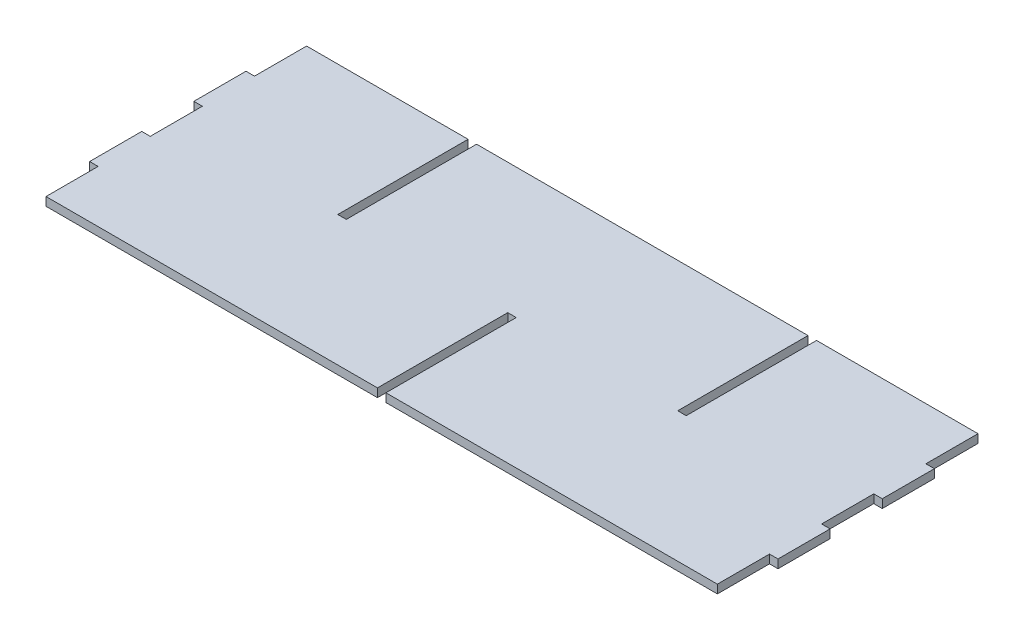
SolidWorks part; units mm, degrees
ref_plane "Piano frontale" through (0, 0, 0) normal (0, 0, 1) x (1, 0, 0)
ref_plane "Piano superiore" through (0, 0, 0) normal (0, 1, 0) x (1, 0, 0)
ref_plane "Piano destro" through (0, 0, 0) normal (1, 0, 0) x (0, 0, -1)
sketch "Schizzo4" plane through (0, 0, 0) normal (0, 1, 0) x (1, 0, 0)
  line L0 (61.5, 46) -> (61.5, -46) construction
  line L2 (-118.5, -46) -> (-118.5, 46) construction
  line L3 (-61.5, 46) -> (-118.5, 46)
  line L4 (118.5, -46) -> (118.5, 46) construction
  line L5 (-118.5, -46) -> (118.5, 46) construction
  line L6 (-118.5, 46) -> (118.5, -46) construction
  line L7 (58.5, 46) -> (58.5, -46) construction
  line L8 (1.5, 46) -> (1.5, -46) construction
  line L9 (-1.5, 46) -> (-1.5, -46) construction
  line L10 (-58.5, 46) -> (-58.5, -46) construction
  line L11 (-61.5, 46) -> (-61.5, -46) construction
  line L12 (-118.5, 46) -> (-118.5, -46) construction
  line L14 (58.5, 46) -> (1.5, 46) construction
  line L15 (-118.5, 0) -> (118.5, 0) construction
  line L19 (-61.5, 46) -> (-61.5, 0)
  line L20 (-61.5, 0) -> (-58.5, 0)
  line L21 (-58.5, 0) -> (-58.5, 46)
  line L22 (-118.5, -46) -> (-1.5, -46)
  line L23 (-58.5, 46) -> (58.5, 46)
  line L24 (1.5, -46) -> (118.5, -46)
  line L25 (61.5, 46) -> (118.5, 46)
  line L26 (-1.5, -46) -> (-1.5, 0)
  line L27 (-1.5, 0) -> (1.5, 0)
  line L28 (1.5, 0) -> (1.5, -46)
  line L29 (58.5, 46) -> (58.5, 0)
  line L30 (58.5, 0) -> (61.5, 0)
  line L31 (61.5, 0) -> (61.5, 46)
  line L32 (-118.5, -46) -> (-118.5, -27.6)
  line L33 (-118.5, -27.6) -> (-121.5, -27.6)
  line L34 (-121.5, -27.6) -> (-121.5, -9.2)
  line L35 (-121.5, -9.2) -> (-118.5, -9.2)
  line L36 (-118.5, -9.2) -> (-118.5, 9.2)
  line L37 (-118.5, 9.2) -> (-121.5, 9.2)
  line L38 (-121.5, 9.2) -> (-121.5, 27.6)
  line L39 (-121.5, 27.6) -> (-118.5, 27.6)
  line L40 (-118.5, 27.6) -> (-118.5, 46)
  line L41 (0, 46) -> (0, -46) construction
  line L42 (118.5, 27.6) -> (118.5, 46)
  line L43 (121.5, 27.6) -> (118.5, 27.6)
  line L44 (121.5, 9.2) -> (121.5, 27.6)
  line L45 (118.5, 9.2) -> (121.5, 9.2)
  line L46 (118.5, -9.2) -> (118.5, 9.2)
  line L47 (121.5, -9.2) -> (118.5, -9.2)
  line L48 (121.5, -27.6) -> (121.5, -9.2)
  line L49 (118.5, -27.6) -> (121.5, -27.6)
  line L50 (118.5, -46) -> (118.5, -27.6)
  line L51 (-121.5, 46) -> (-121.5, -46) construction
  point P0 (0, 0)
  dimension "D1" = 92
  dimension "D2" = 57
  dimension "D3" = 3
  dimension "D5" = 57
  dimension "D7" = 3
  dimension "D4" = 4
extrude "Estrusione-Estrusione1" add sketch "Schizzo4" along normal mid plane 3
